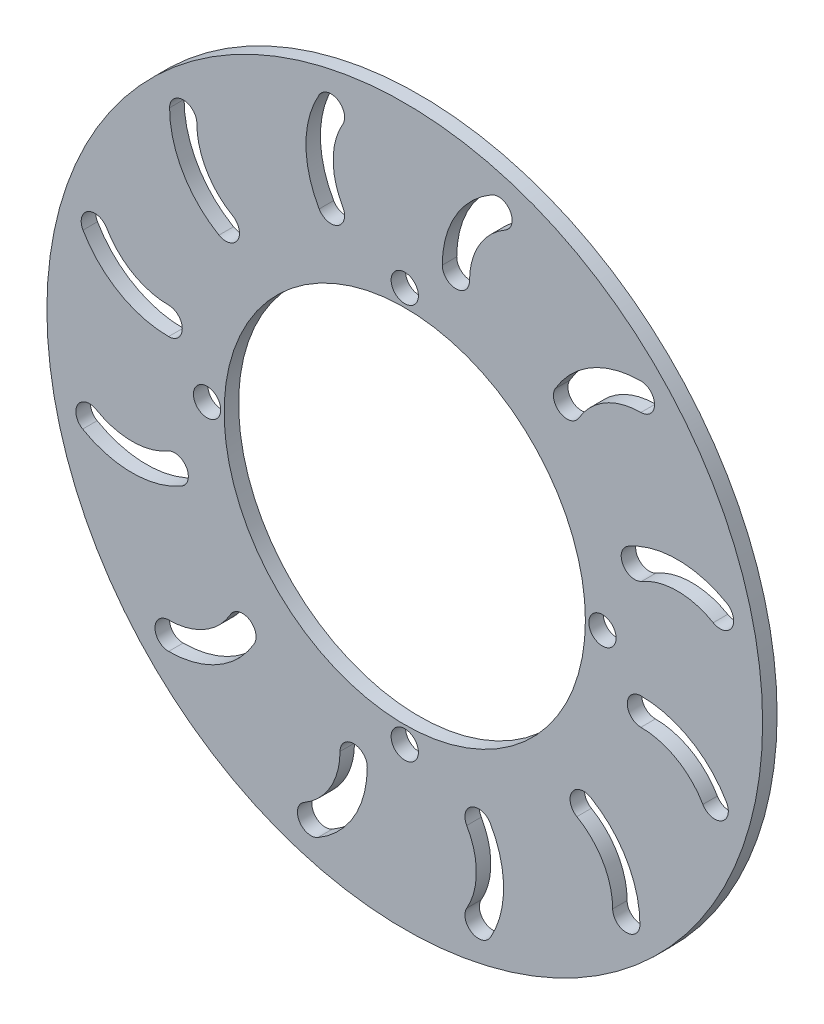
SolidWorks part; units mm, degrees
ref_plane "Front Plane" through (0, 0, 0) normal (0, 0, 1) x (1, 0, 0)
ref_plane "Top Plane" through (0, 0, 0) normal (0, 1, 0) x (1, 0, 0)
ref_plane "Right Plane" through (0, 0, 0) normal (1, 0, 0) x (0, 0, -1)
sketch "Sketch1" plane through (0, 0, 0) normal (0, 0, 1) x (1, 0, 0)
  line L0 (0, 0) -> (0, -50000) construction
  line L1 (4.9217, 0) -> (50004.9217, 0) construction
  line L2 (80, 0) -> (80, 25) construction
  circle A0 centre (0, 0) radius 105
  circle A1 centre (0, 0) radius 53
  circle A2 centre (0, 0) radius 58 construction
  circle A3 centre (0, 0) radius 95 construction
  circle A5 centre (0, 58) radius 4
  circle A8 centre (58, 0) radius 4
  circle A9 centre (0, -58) radius 4
  circle A10 centre (-58, 0) radius 4
  arc A25 (92.5, 21.6506) -> (67.5, 21.6506) centre (80, 0) ccw construction
  arc A26 (94.5, 25.1147) -> (65.5, 25.1147) centre (80, 0) ccw
  arc A27 (90.5, 18.1865) -> (69.5, 18.1865) centre (80, 0) ccw
  arc A28 (90.5, 18.1865) -> (94.5, 25.1147) centre (92.5, 21.6506) ccw
  arc A29 (65.5, 25.1147) -> (69.5, 18.1865) centre (67.5, 21.6506) ccw
  arc A30 (90.9327, -27.5) -> (69.282, -15) centre (69.282, -40) ccw construction
  arc A31 (94.3968, -25.5) -> (69.282, -11) centre (69.282, -40) ccw
  arc A32 (87.4686, -29.5) -> (69.282, -19) centre (69.282, -40) ccw
  arc A33 (87.4686, -29.5) -> (94.3968, -25.5) centre (90.9327, -27.5) ccw
  arc A34 (69.282, -11) -> (69.282, -19) centre (69.282, -15) ccw
  arc A35 (65, -69.282) -> (52.5, -47.6314) centre (40, -69.282) ccw construction
  arc A36 (69, -69.282) -> (54.5, -44.1673) centre (40, -69.282) ccw
  arc A37 (61, -69.282) -> (50.5, -51.0955) centre (40, -69.282) ccw
  arc A38 (61, -69.282) -> (69, -69.282) centre (65, -69.282) ccw
  arc A39 (54.5, -44.1673) -> (50.5, -51.0955) centre (52.5, -47.6314) ccw
  arc A40 (21.6506, -92.5) -> (21.6506, -67.5) centre (0, -80) ccw construction
  arc A41 (25.1147, -94.5) -> (25.1147, -65.5) centre (0, -80) ccw
  arc A42 (18.1865, -90.5) -> (18.1865, -69.5) centre (0, -80) ccw
  arc A43 (18.1865, -90.5) -> (25.1147, -94.5) centre (21.6506, -92.5) ccw
  arc A44 (25.1147, -65.5) -> (18.1865, -69.5) centre (21.6506, -67.5) ccw
  arc A45 (-27.5, -90.9327) -> (-15, -69.282) centre (-40, -69.282) ccw construction
  arc A46 (-25.5, -94.3968) -> (-11, -69.282) centre (-40, -69.282) ccw
  arc A47 (-29.5, -87.4686) -> (-19, -69.282) centre (-40, -69.282) ccw
  arc A48 (-29.5, -87.4686) -> (-25.5, -94.3968) centre (-27.5, -90.9327) ccw
  arc A49 (-11, -69.282) -> (-19, -69.282) centre (-15, -69.282) ccw
  arc A50 (-69.282, -65) -> (-47.6314, -52.5) centre (-69.282, -40) ccw construction
  arc A51 (-69.282, -69) -> (-44.1673, -54.5) centre (-69.282, -40) ccw
  arc A52 (-69.282, -61) -> (-51.0955, -50.5) centre (-69.282, -40) ccw
  arc A53 (-69.282, -61) -> (-69.282, -69) centre (-69.282, -65) ccw
  arc A54 (-44.1673, -54.5) -> (-51.0955, -50.5) centre (-47.6314, -52.5) ccw
  arc A55 (-92.5, -21.6506) -> (-67.5, -21.6506) centre (-80, 0) ccw construction
  arc A56 (-94.5, -25.1147) -> (-65.5, -25.1147) centre (-80, 0) ccw
  arc A57 (-90.5, -18.1865) -> (-69.5, -18.1865) centre (-80, 0) ccw
  arc A58 (-90.5, -18.1865) -> (-94.5, -25.1147) centre (-92.5, -21.6506) ccw
  arc A59 (-65.5, -25.1147) -> (-69.5, -18.1865) centre (-67.5, -21.6506) ccw
  arc A60 (-90.9327, 27.5) -> (-69.282, 15) centre (-69.282, 40) ccw construction
  arc A61 (-94.3968, 25.5) -> (-69.282, 11) centre (-69.282, 40) ccw
  arc A62 (-87.4686, 29.5) -> (-69.282, 19) centre (-69.282, 40) ccw
  arc A63 (-87.4686, 29.5) -> (-94.3968, 25.5) centre (-90.9327, 27.5) ccw
  arc A64 (-69.282, 11) -> (-69.282, 19) centre (-69.282, 15) ccw
  arc A65 (-65, 69.282) -> (-52.5, 47.6314) centre (-40, 69.282) ccw construction
  arc A66 (-69, 69.282) -> (-54.5, 44.1673) centre (-40, 69.282) ccw
  arc A67 (-61, 69.282) -> (-50.5, 51.0955) centre (-40, 69.282) ccw
  arc A68 (-61, 69.282) -> (-69, 69.282) centre (-65, 69.282) ccw
  arc A69 (-54.5, 44.1673) -> (-50.5, 51.0955) centre (-52.5, 47.6314) ccw
  arc A70 (-21.6506, 92.5) -> (-21.6506, 67.5) centre (0, 80) ccw construction
  arc A71 (-25.1147, 94.5) -> (-25.1147, 65.5) centre (0, 80) ccw
  arc A72 (-18.1865, 90.5) -> (-18.1865, 69.5) centre (0, 80) ccw
  arc A73 (-18.1865, 90.5) -> (-25.1147, 94.5) centre (-21.6506, 92.5) ccw
  arc A74 (-25.1147, 65.5) -> (-18.1865, 69.5) centre (-21.6506, 67.5) ccw
  arc A75 (27.5, 90.9327) -> (15, 69.282) centre (40, 69.282) ccw construction
  arc A76 (25.5, 94.3968) -> (11, 69.282) centre (40, 69.282) ccw
  arc A77 (29.5, 87.4686) -> (19, 69.282) centre (40, 69.282) ccw
  arc A78 (29.5, 87.4686) -> (25.5, 94.3968) centre (27.5, 90.9327) ccw
  arc A79 (11, 69.282) -> (19, 69.282) centre (15, 69.282) ccw
  arc A80 (69.282, 65) -> (47.6314, 52.5) centre (69.282, 40) ccw construction
  arc A81 (69.282, 69) -> (44.1673, 54.5) centre (69.282, 40) ccw
  arc A82 (69.282, 61) -> (51.0955, 50.5) centre (69.282, 40) ccw
  arc A83 (69.282, 61) -> (69.282, 69) centre (69.282, 65) ccw
  arc A84 (44.1673, 54.5) -> (51.0955, 50.5) centre (47.6314, 52.5) ccw
  point P27 (81.782, -18.3494)
  point P35 (61.6506, -56.782)
  point P44 (25, -80)
  point P52 (-18.3494, -81.782)
  point P54 (80, 25)
  point P65 (-56.782, -61.6506)
  point P73 (-80, -25)
  point P81 (-81.782, 18.3494)
  point P89 (-61.6506, 56.782)
  point P97 (-25, 80)
  point P105 (18.3494, 81.782)
  point P113 (56.782, 61.6506)
  dimension "D1" = 210
  dimension "D2" = 116
  dimension "D3" = 106
  dimension "D4" = 190
  dimension "D5" = 12
  dimension "D6" = 8
  dimension "D12" = 4
  dimension "D13" = 25
  dimension "D14" = 25
  dimension "D9" = 4
extrude "Boss-Extrude1" add sketch "Sketch1" along normal blind 4.25
